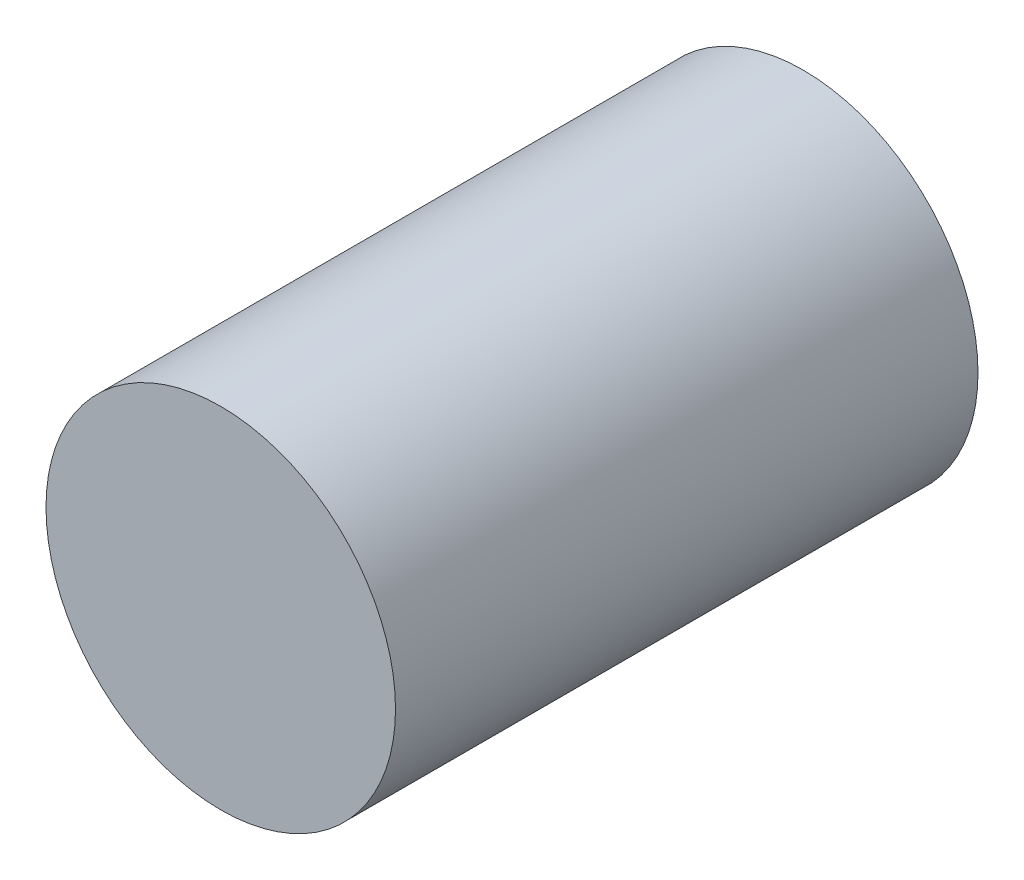
SolidWorks part; units mm, degrees
ref_plane "前视基准面" through (0, 0, 0) normal (0, 0, 1) x (1, 0, 0)
ref_plane "上视基准面" through (0, 0, 0) normal (0, 1, 0) x (1, 0, 0)
ref_plane "右视基准面" through (0, 0, 0) normal (1, 0, 0) x (0, 0, -1)
sketch "草图1" plane through (0, 0, 0) normal (0, 0, 1) x (1, 0, 0)
  circle A0 centre (1.5543, 0) radius 0.3
extrude "凸台-拉伸1" add sketch "草图1" along normal blind 1
